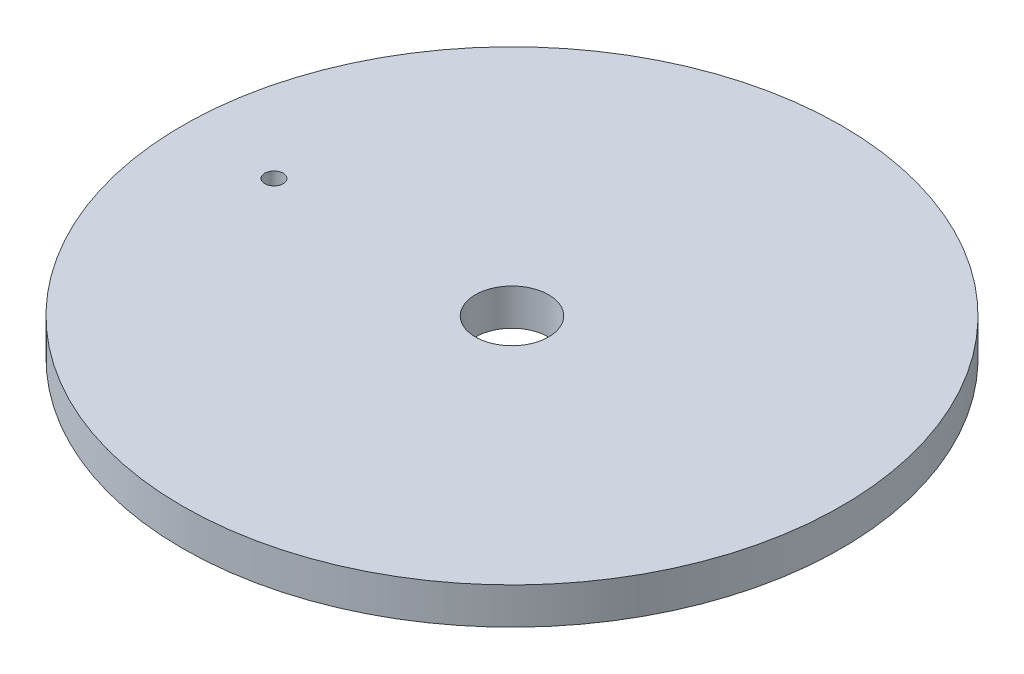
SolidWorks part; units mm, degrees
ref_plane "Front Plane" through (0, 0, 0) normal (0, 0, 1) x (1, 0, 0)
ref_plane "Top Plane" through (0, 0, 0) normal (0, 1, 0) x (1, 0, 0)
ref_plane "Right Plane" through (0, 0, 0) normal (1, 0, 0) x (0, 0, -1)
sketch "Sketch1" plane through (0, 0, 0) normal (0, 0, 1) x (1, 0, 0)
  line L0 (-6.35, 0) -> (-52.5145, 0)
  line L1 (-57.15, 0) -> (-57.15, 6.35)
  line L6 (-57.15, 6.35) -> (-6.35, 6.35)
  line L7 (-6.35, 6.35) -> (-6.35, 0)
  line L8 (0, 0) -> (0, 9.974) construction
  line L9 (-57.15, 0) -> (-55.5625, 0)
  line L10 (-55.5625, 0) -> (-55.5625, 2.032)
  line L11 (-55.5625, 2.032) -> (-52.5145, 2.032)
  line L12 (-52.5145, 2.032) -> (-52.5145, 0)
  dimension "D1" = 6.35
  dimension "D2" = 2.032
  dimension "D3" = 1.5875
  dimension "D4" = 3.048
  dimension "D5" = 6.35
  dimension "D6" = 57.15
revolve "Revolve1" add sketch "Sketch1" angle 360 about L8
hole_wizard "1/8 (0.125) Diameter Hole1" positions "Sketch2" profile "Sketch3" hole size "1/8" standard "ANSI Inch"
sketch "Sketch2" plane through (0, 6.35, 0) normal (0, 1, 0) x (1, 0, 0)
  point P0 (-41.275, 0)
  dimension "D1" = 41.275
sketch "Sketch3" plane through (-41.275, 6.35, 0) normal (1, 0, 0) x (0, 0, 1)
  line L0 (0, 0) -> (0, 4.1289)
  line L1 (0, 4.1289) -> (1.5875, 3.175)
  line L2 (1.5875, 3.175) -> (1.5875, 0)
  line L5 (1.5875, 0) -> (0, 0)
  line L10 (0, 4.1289) -> (-1.5875, 3.175) construction
  line L11 (0, -6.35) -> (0, 107.95) construction
  dimension "Hole Dia." = 3.175
  dimension "Hole Depth" = 3.175
  dimension "Drill Angle" = 118
